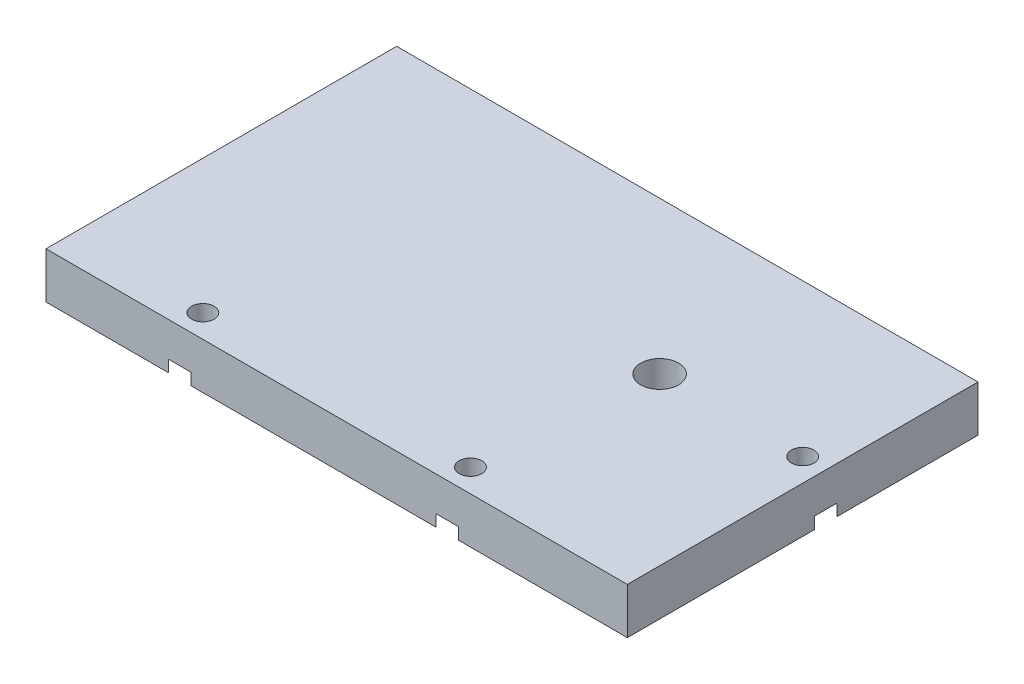
SolidWorks part; units mm, degrees
ref_plane "Front Plane" through (0, 0, 0) normal (0, 0, 1) x (1, 0, 0)
ref_plane "Top Plane" through (0, 0, 0) normal (0, 1, 0) x (1, 0, 0)
ref_plane "Right Plane" through (0, 0, 0) normal (1, 0, 0) x (0, 0, -1)
sketch "Sketch1" plane through (0, 0, 0) normal (0, 1, 0) x (1, 0, 0)
  line L1 (-31.5, 19) -> (31.5, 19)
  line L2 (-31.5, 19) -> (-31.5, -19)
  line L3 (-31.5, -19) -> (31.5, -19)
  line L4 (31.5, 19) -> (31.5, -19)
extrude "Boss-Extrude1" add sketch "Sketch1" along normal blind 5
sketch "Sketch4" plane through (0, 0, 0) normal (0, -1, 0) x (-1, 0, 0)
  line L0 (-31.5, 19) -> (-26.5, 19)
  line L1 (-31.5, 19) -> (31.5, 19) construction
  line L2 (-31.5, -19) -> (-26.5, -19)
  line L3 (31.5, -19) -> (-31.5, -19) construction
  line L4 (-26.5, -19) -> (-26.5, 19)
  line L5 (-31.5, -19) -> (-31.5, -14)
  line L6 (-31.5, -19) -> (-31.5, 19) construction
  line L7 (-31.5, -14) -> (-26.5, -14)
  line L8 (-31.5, 19) -> (-26.5, -14)
  line L9 (-31.5, -14) -> (-26.5, 19)
hole_wizard "CBORE for #2 Binding Head Machine Screw2" positions "Sketch8" profile "Sketch9" counterbore size "#2" standard "ANSI Inch" end condition through all
sketch "Sketch8" plane through (0, 0, 0) normal (0, -1, 0) x (-1, 0, 0)
  line L0 (-31.5, 19) -> (-26.5, -14) construction
  point P0 (-29, 2.5)
sketch "Sketch9" plane through (29, 0, -2.5) normal (1, 0, 0) x (0, 0, -1)
  line L0 (0, 0) -> (0, 5)
  line L1 (0, 5) -> (1.2192, 5)
  line L3 (1.2192, 5) -> (1.2192, 1.27)
  line L4 (1.2192, 1.27) -> (2.7788, 1.27)
  line L5 (2.7788, 1.27) -> (2.7788, 0)
  line L7 (2.7788, 0) -> (0, 0)
  line L11 (0, -6.35) -> (0, 107.95) construction
  dimension "Thru Hole Dia." = 2.4384
  dimension "Thru Hole Depth" = 5
  dimension "C'Bore Dia." = 5.5575
  dimension "C'Bore Depth" = 1.27
sketch "Sketch10" plane through (0, 0, 0) normal (0, -1, 0) x (-1, 0, 0)
  line L0 (-26.5, -14) -> (31.5, -14)
  line L1 (31.5, 19) -> (31.5, -19) construction
  line L2 (31.5, -14) -> (-26.5, -19)
  line L3 (31.5, -19) -> (-26.5, -14)
  line L4 (2.5, -16.5) -> (2.5, -19)
  line L5 (31.5, -19) -> (-31.5, -19) construction
  line L6 (2.5, -16.5) -> (2.5, -14)
  line L7 (31.5, -19) -> (2.5, -14)
  line L8 (2.5, -19) -> (31.5, -14)
  line L9 (2.5, -19) -> (-26.5, -14)
  line L10 (2.5, -14) -> (-26.5, -19)
hole_wizard "CBORE for #2 Binding Head Machine Screw3" positions "Sketch11" profile "Sketch12" counterbore size "#2" standard "ANSI Inch" end condition through all
sketch "Sketch11" plane through (0, 0, 0) normal (0, -1, 0) x (-1, 0, 0)
  line L0 (2.5, -19) -> (-26.5, -14) construction
  line L1 (31.5, -19) -> (2.5, -14) construction
  point P0 (-12, -16.5)
  point P4 (17, -16.5)
sketch "Sketch12" plane through (12, 0, 16.5) normal (1, 0, 0) x (0, 0, -1)
  line L0 (0, 0) -> (0, 5)
  line L1 (0, 5) -> (1.2192, 5)
  line L3 (1.2192, 5) -> (1.2192, 1.27)
  line L4 (1.2192, 1.27) -> (2.7788, 1.27)
  line L5 (2.7788, 1.27) -> (2.7788, 0)
  line L7 (2.7788, 0) -> (0, 0)
  line L11 (0, -6.35) -> (0, 107.95) construction
  dimension "Thru Hole Dia." = 2.4384
  dimension "Thru Hole Depth" = 5
  dimension "C'Bore Dia." = 5.5575
  dimension "C'Bore Depth" = 1.27
sketch "Sketch13" plane through (0, 0, -19) normal (0, 0, -1) x (-1, 0, 0)
  line L0 (-26.2212, 0) -> (-26.2212, 5)
  line L1 (-31.5, 5) -> (31.5, 5) construction
  line L2 (-26.2212, 5) -> (31.5, 0)
  line L3 (31.5, 0) -> (31.5, 5)
  line L4 (31.5, 5) -> (-26.2212, 0)
  line L5 (2.6394, 2.5) -> (2.6394, 0)
  line L8 (2.5, 0) -> (31.5, 0) construction
  line L9 (2.6394, 2.5) -> (2.6394, 5)
  line L10 (-26.2212, 5) -> (2.6394, 0)
  line L11 (2.6394, 0) -> (31.5, 5)
  line L12 (-26.2212, 0) -> (2.6394, 5)
  line L13 (2.6394, 5) -> (31.5, 0)
sketch "Sketch17" plane through (0, 0, 0) normal (0, -1, 0) x (1, 0, 0)
  line L1 (13.5, -19) -> (31.5, -19)
  line L3 (31.5, -19) -> (-31.5, -19) construction
  line L7 (13.5, 14) -> (13.5, -19)
  line L8 (13.5, -19) -> (13.5, -2.5)
  circle A0 centre (13.5, -2.5) radius 2.05
extrude "Cut-Extrude1" cut sketch "Sketch17" against normal blind 10 contours L7 A0 | L7 A0
sketch "Sketch19" plane through (0, 0, 0) normal (0, -1, 0) x (1, 0, 0)
  line L0 (13.5, -2.5) -> (13.5, -8.6)
  line L1 (13.5, -2.5) -> (13.5, 3.6)
hole_wizard "#2-56 Tapped Hole2" positions "Sketch21" profile "Sketch22" tap size "#2-56" standard "ANSI Inch"
sketch "Sketch21" plane through (0, 0, 0) normal (0, -1, 0) x (-1, 0, 0)
  point P0 (-13.5, 8.6)
  point P3 (-13.5, -3.6)
sketch "Sketch22" plane through (13.5, 0, -8.6) normal (1, 0, 0) x (0, 0, -1)
  line L0 (0, 0) -> (0, 3)
  line L1 (0, 3) -> (0.889, 2.4658)
  line L2 (0.889, 2.4658) -> (0.889, 0)
  line L5 (0.889, 0) -> (0, 0)
  line L10 (0, 3) -> (-0.889, 2.4658) construction
  line L11 (0, -6.35) -> (0, 107.95) construction
  dimension "Tap Drill Dia." = 1.778
  dimension "Tap Drill Depth" = 3
  dimension "Drill Angle" = 118
cosmetic thread "Hole Thread3" parameters "D1"=3, "D2"=2.1844
cosmetic thread "Hole Thread4" parameters "D1"=3, "D2"=2.1844
sketch "Sketch25" plane through (0, 0, -19) normal (0, 0, -1) x (-1, 0, 0)
  line L0 (31.5, 2.5) -> (17, 2.5)
  line L1 (31.5, 5) -> (31.5, 0) construction
  line L2 (31.5, 2.5) -> (-12, 2.5)
hole_wizard "#2-56 Tapped Hole3" positions "Sketch26" profile "Sketch27" tap size "#2-56" standard "ANSI Inch"
sketch "Sketch26" plane through (0, 0, -19) normal (0, 0, -1) x (-1, 0, 0)
  point P0 (-12, 2.5)
  point P3 (17, 2.5)
sketch "Sketch27" plane through (12, 2.5, -19) normal (1, 0, 0) x (0, 1, 0)
  line L0 (0, 0) -> (0, 8)
  line L1 (0, 8) -> (0.889, 7.4658)
  line L2 (0.889, 7.4658) -> (0.889, 0)
  line L5 (0.889, 0) -> (0, 0)
  line L10 (0, 8) -> (-0.889, 7.4658) construction
  line L11 (0, -6.35) -> (0, 107.95) construction
  dimension "Tap Drill Dia." = 1.778
  dimension "Tap Drill Depth" = 8
  dimension "Drill Angle" = 118
cosmetic thread "Hole Thread5" parameters "D1"=8, "D2"=2.1844
cosmetic thread "Hole Thread6" parameters "D1"=8, "D2"=2.1844
